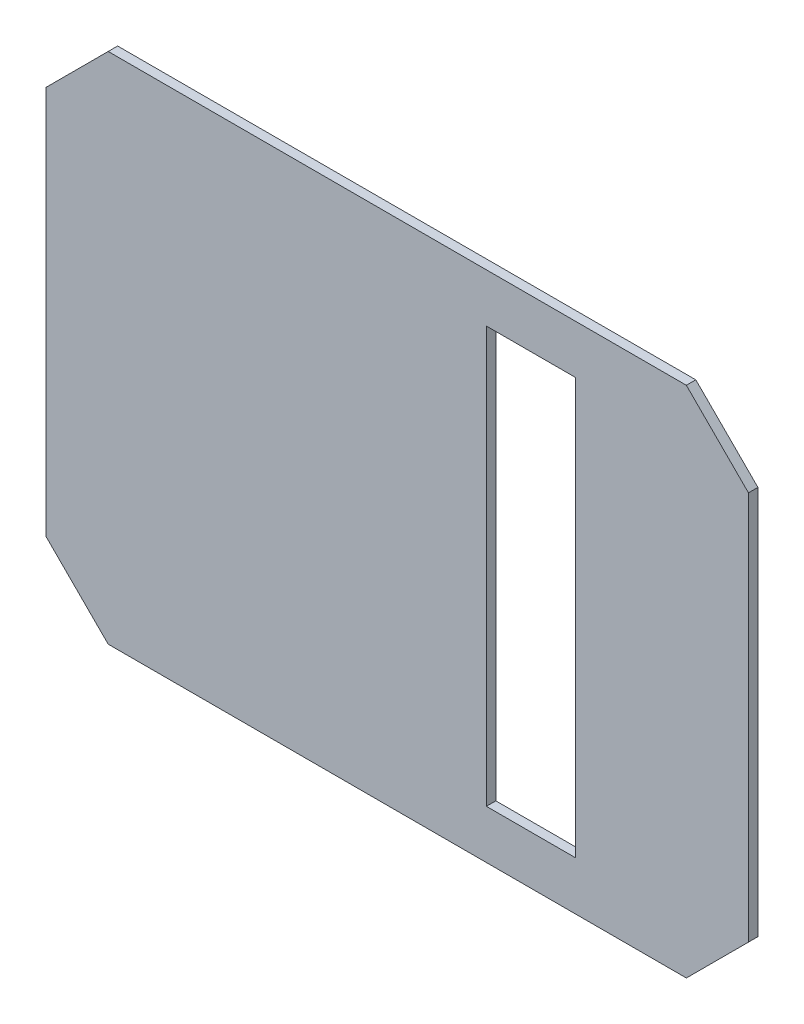
SolidWorks part; units mm, degrees
material "Thornel Mat VMA"
ref_plane "Front Plane" through (0, 0, 0) normal (0, 0, 1) x (1, 0, 0)
ref_plane "Top Plane" through (0, 0, 0) normal (0, 1, 0) x (1, 0, 0)
ref_plane "Right Plane" through (0, 0, 0) normal (1, 0, 0) x (0, 0, -1)
sketch "Sketch1" plane through (0, 0, 0) normal (0, 0, 1) x (1, 0, 0)
  line L5 (107.95, 76.2) -> (107.4471, 75.845) construction
  line L6 (107.95, -76.2) -> (107.4471, -75.845) construction
  line L12 (97.0921, -86.2) -> (-97.0921, -86.2)
  line L13 (-97.0921, -86.2) -> (-117.95, -65.3421)
  line L14 (-117.95, 65.3421) -> (-117.95, -65.3421)
  line L15 (-97.0921, 86.2) -> (-117.95, 65.3421)
  line L16 (97.0921, 86.2) -> (-97.0921, 86.2)
  line L17 (117.95, 65.3421) -> (97.0921, 86.2)
  line L18 (117.95, 65.3421) -> (117.95, -65.3421)
  line L19 (117.95, -65.3421) -> (97.0921, -86.2)
  line L27 (-107.4471, 75.845) -> (-107.95, 76.2) construction
  line L31 (-107.4471, -75.845) -> (-107.95, -76.2) construction
  point P0 (0, 0)
extrude "Boss-Extrude1" add sketch "Sketch1" along normal blind 3.175
sketch "Sketch5" plane through (0, 0, 3.175) normal (0, 0, 1) x (1, 0, 0)
  line L1 (59.925, 69.85) -> (29.925, 69.85)
  line L2 (59.925, 69.85) -> (59.925, -69.85)
  line L3 (59.925, -69.85) -> (29.925, -69.85)
  line L4 (29.925, 69.85) -> (29.925, -69.85)
  line L5 (59.925, 69.85) -> (29.925, -69.85) construction
  line L6 (59.925, -69.85) -> (29.925, 69.85) construction
  line L7 (-117.95, 65.3421) -> (-117.95, -65.3421) construction
  line L8 (105.2784, 95.25) -> (-105.2784, 95.25) construction
  line L9 (117.95, -65.3421) -> (117.95, 65.3421) construction
  point P0 (44.925, 0)
  point P8 (-117.95, 0)
  dimension "D1" = 25.4
  dimension "D2" = 30
  dimension "D3" = 73.025
extrude "Cut-Extrude7" cut sketch "Sketch5" against normal blind 3.175
